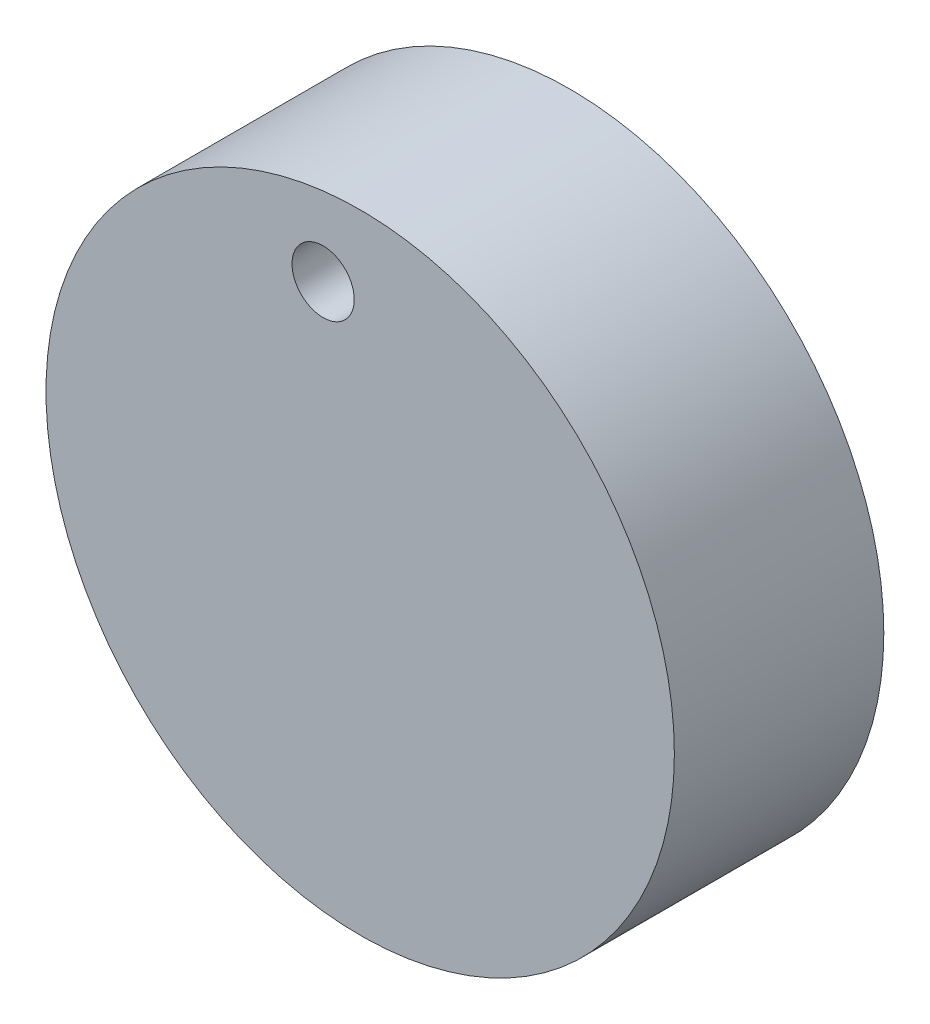
SolidWorks part; units mm, degrees
ref_plane "Front Plane" through (0, 0, 0) normal (0, 0, 1) x (1, 0, 0)
ref_plane "Top Plane" through (0, 0, 0) normal (0, 1, 0) x (1, 0, 0)
ref_plane "Right Plane" through (0, 0, 0) normal (1, 0, 0) x (0, 0, -1)
sketch "Sketch1" plane through (0, 0, 0) normal (0, 0, 1) x (1, 0, 0)
  circle A0 centre (0, 0) radius 9
  dimension "D1" = 18
extrude "Extrude1" add sketch "Sketch1" along normal blind 6
sketch "Sketch2" plane through (0, 0, 6) normal (0, 0, 1) x (1, 0, 0)
  circle A0 centre (-1.0618, 6.6839) radius 0.8914
extrude "Extrude2" cut sketch "Sketch2" against normal through all
